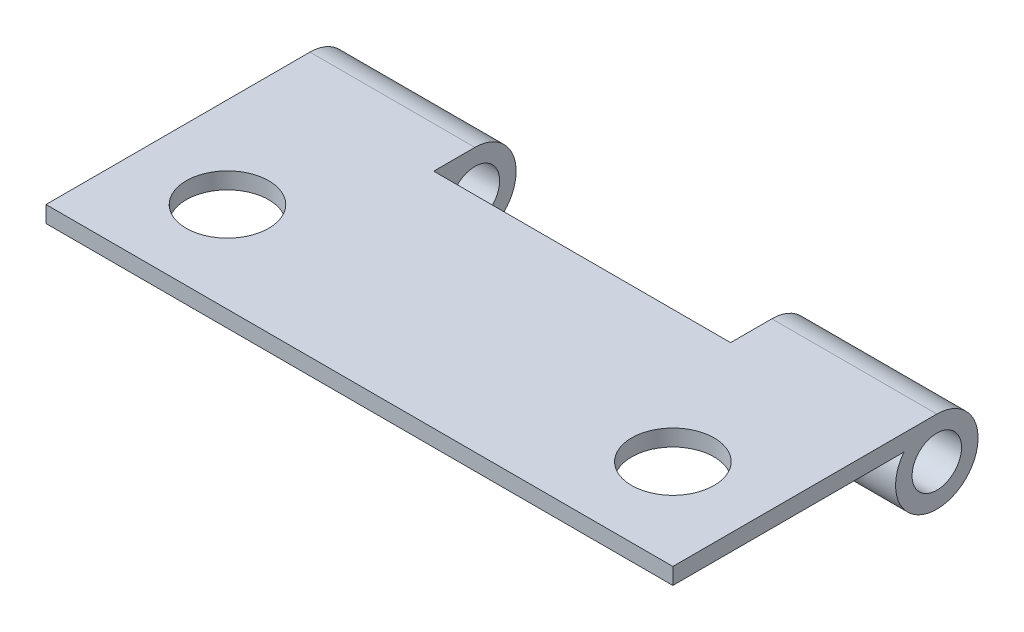
SolidWorks part; units mm, degrees
ref_plane "Front Plane" through (0, 0, 0) normal (0, 0, 1) x (1, 0, 0)
ref_plane "Top Plane" through (0, 0, 0) normal (0, 1, 0) x (1, 0, 0)
ref_plane "Right Plane" through (0, 0, 0) normal (1, 0, 0) x (0, 0, -1)
sketch "Sketch3" plane through (0, 0, 0) normal (1, 0, 0) x (0, 0, -1)
  line L0 (16, 1) -> (0, 1)
  line L1 (0, 0) -> (14, 0)
  line L2 (0, 0) -> (0, 1)
  arc A0 (16, 1) -> (14, 0) centre (16, -1.5) cw
  circle A1 centre (16, -1.5) radius 1.5
  dimension "D3" = 3
  dimension "D1" = 1
  dimension "D2" = 14
extrude "Boss-Extrude2" add sketch "Sketch3" along normal blind 38
sketch "Sketch6" plane through (0, 1, 0) normal (0, 1, 0) x (1, 0, 0)
  line L0 (38, 16) -> (0, 16) construction
  line L1 (10, 13.5) -> (28, 13.5)
  line L2 (10, 13.5) -> (10, 18.5)
  line L3 (10, 18.5) -> (28, 18.5)
  line L4 (28, 13.5) -> (28, 18.5)
  line L5 (0, 16) -> (0, 0) construction
  line L6 (38, 16) -> (38, 0) construction
  dimension "D1" = 2.5
  dimension "D2" = 5
  dimension "D3" = 10
  dimension "D4" = 10
extrude "Cut-Extrude1" cut sketch "Sketch6" against normal through all
sketch "Sketch7" plane through (0, 1, 0) normal (0, 1, 0) x (1, 0, 0)
  line L0 (19, 0) -> (19, 13.5) construction
  line L1 (38, 0) -> (0, 0) construction
  line L2 (10, 13.5) -> (28, 13.5) construction
  line L3 (0, 16) -> (0, 0) construction
  circle A0 centre (5.5, 5.5) radius 2.5
  circle A1 centre (32.5, 5.5) radius 2.5
  dimension "D1" = 5
  dimension "D2" = 5.5
  dimension "D3" = 5.5
extrude "Cut-Extrude2" cut sketch "Sketch7" against normal blind 10
